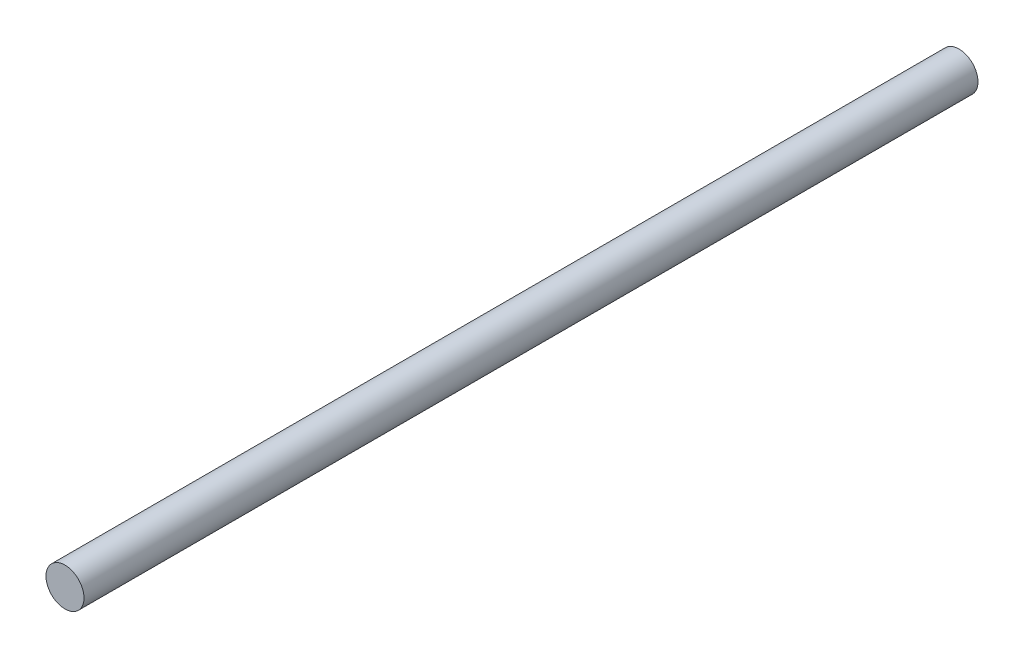
SolidWorks part; units mm, degrees
ref_plane "前视基准面" through (0, 0, 0) normal (0, 0, 1) x (1, 0, 0)
ref_plane "上视基准面" through (0, 0, 0) normal (0, 1, 0) x (1, 0, 0)
ref_plane "右视基准面" through (0, 0, 0) normal (1, 0, 0) x (0, 0, -1)
sketch "草图1" plane through (0, 0, 0) normal (0, 0, 1) x (1, 0, 0)
  circle A0 centre (0, 0) radius 2
extrude "凸台-拉伸1" add sketch "草图1" along normal blind 94
cosmetic thread "装饰螺纹线1" parameters "D1"=16, "D2"=3.242
